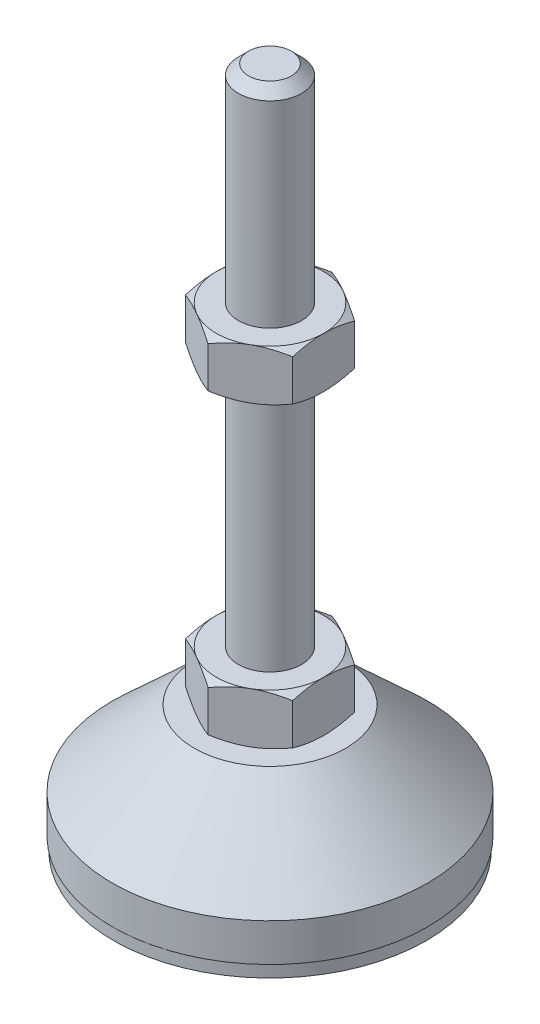
SolidWorks part; units mm, degrees
ref_plane "Спереди" through (0, 0, 0) normal (0, 0, 1) x (1, 0, 0)
ref_plane "Сверху" through (0, 0, 0) normal (0, 1, 0) x (1, 0, 0)
ref_plane "Справа" through (0, 0, 0) normal (1, 0, 0) x (0, 0, -1)
sketch "Эскиз1" plane through (0, 0, 0) normal (0, 0, 1) x (1, 0, 0)
  line L0 (0, 0) -> (-24.8, 0)
  line L1 (-24.8, 0) -> (-24.8, 2)
  line L2 (-24.8, 2) -> (-25, 2)
  line L3 (-25, 2) -> (-25, 8)
  line L4 (-25, 8) -> (-12, 20)
  line L5 (-12, 20) -> (-5, 20)
  line L12 (-5, 28) -> (-5, 106.4)
  line L13 (-5, 106.4) -> (-3.4, 108)
  line L14 (-3.4, 108) -> (0, 108)
  line L15 (0, 108) -> (0, 0) construction
  line L16 (-5, 20) -> (0, 20) construction
  line L17 (0, 0) -> (0, 108)
  line L18 (0, 0) -> (0, -7.9595) construction
  line L19 (-5, 28) -> (-5, 20)
  point P8 (-5, 67.2)
  point P23 (-8.5, 20)
  dimension "D1" = 10
  dimension "D2" = 20
  dimension "D3" = 8
  dimension "D4" = 50
  dimension "D5" = 5
  dimension "D6" = 1.6
  dimension "D7" = 45
  dimension "D8" = 24
  dimension "D9" = 2
  dimension "D10" = 80
  dimension "D11" = 6
  dimension "D12" = 0.2
revolve "Повернуть1" add sketch "Эскиз1" angle 360 about L17
sketch "Эскиз2" plane through (0, 20, 0) normal (0, 1, 0) x (1, 0, 0)
  line L1 (0, 9.815) -> (-8.5, 4.9075)
  line L2 (-8.5, 4.9075) -> (-8.5, -4.9075)
  line L3 (-8.5, -4.9075) -> (0, -9.815)
  line L4 (0, -9.815) -> (8.5, -4.9075)
  line L5 (8.5, -4.9075) -> (8.5, 4.9075)
  line L6 (8.5, 4.9075) -> (0, 9.815)
  circle A0 centre (0, 0) radius 8.5 construction
  dimension "D1" = 17
extrude "Бобышка-Вытянуть1" add sketch "Эскиз2" along normal up to vertex (8 mm away) up to point (-5, 28, 0)
ref_plane "Плоскость1" through (0, 67.2, 0) normal (0, 1, 0) x (1, 0, 0)
sketch "Эскиз3" plane through (0, 67.2, 0) normal (0, 1, 0) x (1, 0, 0)
  line L6 (8.5, 4.9075) -> (0, 9.815)
  line L7 (0, 9.815) -> (-8.5, 4.9075)
  line L8 (-8.5, 4.9075) -> (-8.5, -4.9075)
  line L9 (-8.5, -4.9075) -> (0, -9.815)
  line L10 (0, -9.815) -> (8.5, -4.9075)
  line L11 (8.5, -4.9075) -> (8.5, 4.9075)
  line L12 (8.5, 4.9075) -> (0, 9.815)
  line L13 (0, 9.815) -> (-8.5, 4.9075)
  line L14 (-8.5, 4.9075) -> (-8.5, -4.9075)
  line L15 (-8.5, -4.9075) -> (0, -9.815)
  line L16 (0, -9.815) -> (8.5, -4.9075)
  line L17 (8.5, -4.9075) -> (8.5, 4.9075)
  dimension "D1" = 0
extrude "Бобышка-Вытянуть2" add sketch "Эскиз3" along normal blind 8
sketch "Эскиз4" plane through (0, 0, 0) normal (0, 0, 1) x (1, 0, 0)
  line L0 (-8.5, 75.2) -> (-15.4282, 71.2)
  line L1 (-15.4282, 71.2) -> (-15.4282, 75.2)
  line L2 (-15.4282, 75.2) -> (-8.5, 75.2)
  line L3 (-15.4282, 71.2) -> (-8.5, 67.2)
  line L4 (50, 67.2) -> (-50, 67.2) construction
  line L5 (-8.5, 67.2) -> (-15.4282, 67.2)
  line L6 (-15.4282, 67.2) -> (-15.4282, 71.2)
  line L7 (-8.5, 75.2) -> (-8.5, 67.2) construction
  line L8 (-8.5, 28) -> (-15.4282, 28)
  line L9 (-15.4282, 28) -> (-15.4282, 24)
  line L10 (-15.4282, 24) -> (-8.5, 28)
  line L11 (-8.5, 20) -> (-15.4282, 24)
  line L12 (-15.4282, 24) -> (-15.4282, 20)
  line L13 (-15.4282, 20) -> (-8.5, 20)
  line L14 (0, 108) -> (0, 96.3793) construction
  dimension "D1" = 30
  dimension "D2" = 30
revolve "Вырез-Повернуть2" cut sketch "Эскиз4" angle 360 about L14
